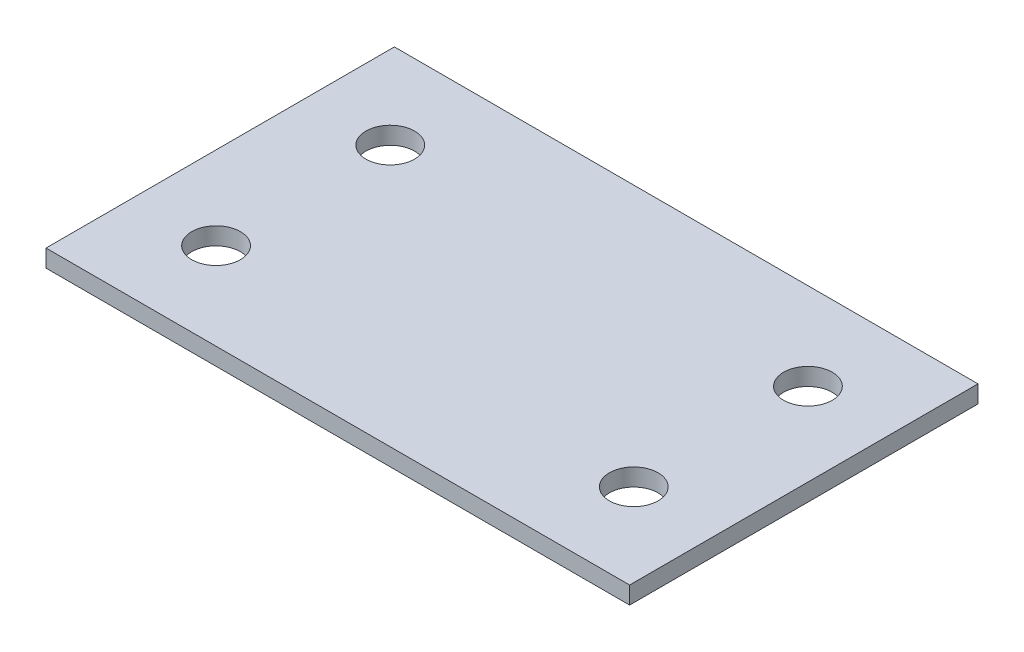
SolidWorks part; units mm, degrees
ref_plane "Front" through (0, 0, 0) normal (0, 0, 1) x (1, 0, 0)
ref_plane "Top" through (0, 0, 0) normal (0, 1, 0) x (1, 0, 0)
ref_plane "Right" through (0, 0, 0) normal (1, 0, 0) x (0, 0, -1)
sketch "Sketch1" plane through (0, 0, 0) normal (0, 0, 1) x (1, 0, 0)
  line L5 (0, 0) -> (2.596, 0)
  line L6 (2.596, 0) -> (29.1712, 0)
  line L8 (29.1712, 0) -> (29.1712, 1)
  line L9 (29.1712, 1) -> (26.5752, 1)
  line L12 (26.5752, 1) -> (0, 1)
  line L13 (0, 1) -> (0, 0)
  dimension "D1" = 1
  dimension "D2" = 2.596
  dimension "D3" = 24
extrude "Boss-Extrude1" add sketch "Sketch1" along normal blind 20
sketch "Sketch6" plane through (0, 1, 0) normal (0, 1, 0) x (1, 0, 0)
  line L2 (26.5752, -15) -> (26.5752, -5) construction
  line L3 (2.596, -15) -> (2.596, -5) construction
  line L4 (26.5752, -10) -> (29.1712, -10) construction
  line L5 (0, -10) -> (2.596, -10) construction
  line L6 (29.1712, -20) -> (29.1712, 0) construction
  line L7 (0, -20) -> (0, 0) construction
  circle A0 centre (26.5752, -15) radius 1.397
  circle A1 centre (2.596, -15) radius 1.397
  circle A2 centre (2.596, -5) radius 1.397
  circle A3 centre (26.5752, -5) radius 1.397
  dimension "D2" = 2.794
  dimension "D1" = 10
  dimension "D3" = 2.596
extrude "Cut-Extrude1" cut sketch "Sketch6" against normal up to surface (1 mm away) up to face at (14.5856, 0, 10)
sketch "Sketch7" plane through (0, 1, 0) normal (0, 1, 0) x (1, 0, 0)
  line L0 (29.1712, 0) -> (0, 0) construction
  line L1 (29.1712, 0) -> (31.3377, 0)
  line L2 (29.1712, 0) -> (29.1712, -20)
  line L3 (29.1712, -20) -> (31.3377, -20)
  line L4 (31.3377, 0) -> (31.3377, -20)
  line L5 (29.1712, -20) -> (0, -20) construction
  line L6 (0, -20) -> (0, 0) construction
  line L7 (0, 0) -> (-2.1665, 0)
  line L8 (0, 0) -> (0, -20)
  line L9 (0, -20) -> (-2.1665, -20)
  line L10 (-2.1665, 0) -> (-2.1665, -20)
  line L11 (0, 0) -> (29.1712, 0) construction
  dimension "D1" = 2.1665
extrude "Boss-Extrude2" add sketch "Sketch7" against normal up to surface (1 mm away) up to face at (25.1782, 0, 5)
